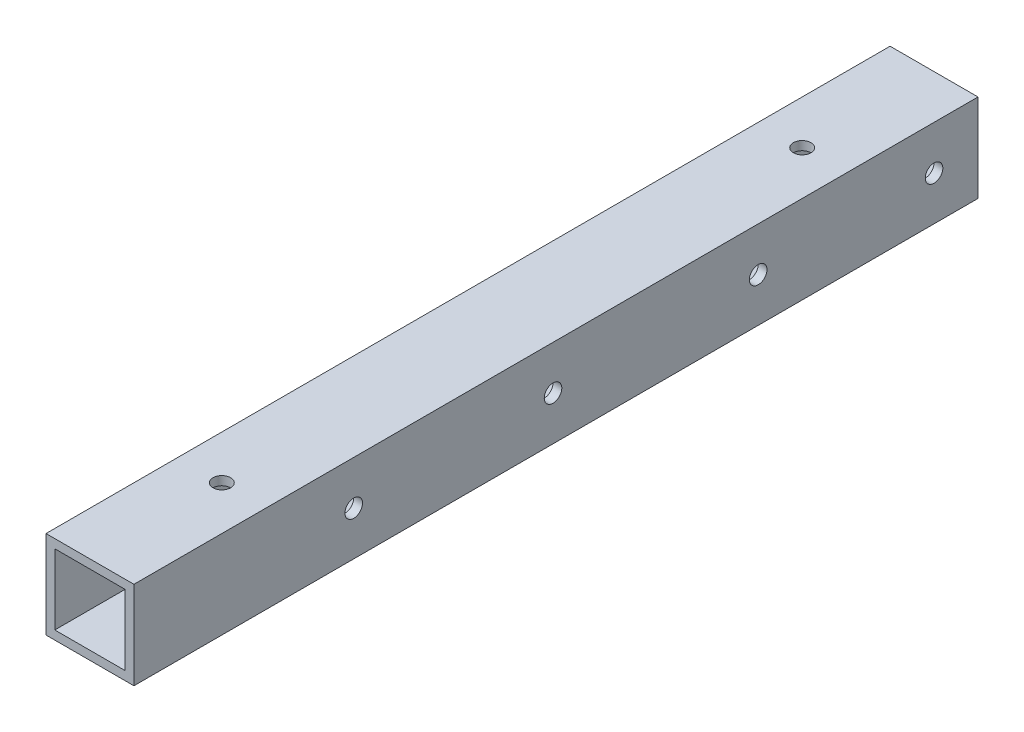
SolidWorks part; units mm, degrees
material "1060 合金"
ref_plane "正面" through (0, 0, 0) normal (0, 0, 1) x (1, 0, 0)
ref_plane "平面" through (0, 0, 0) normal (0, 1, 0) x (1, 0, 0)
ref_plane "右側面" through (0, 0, 0) normal (1, 0, 0) x (0, 0, -1)
sketch "ｽｹｯﾁ1" plane through (0, 0, 0) normal (0, 0, 1) x (1, 0, 0)
  line L1 (-7.0101, 7.7326) -> (7.9899, 7.7326)
  line L2 (-7.0101, 7.7326) -> (-7.0101, -7.2674)
  line L3 (-7.0101, -7.2674) -> (7.9899, -7.2674)
  line L4 (7.9899, 7.7326) -> (7.9899, -7.2674)
  line L9 (-5.5101, 6.2326) -> (6.4899, 6.2326)
  line L10 (-5.5101, 6.2326) -> (-5.5101, -5.7674)
  line L11 (-5.5101, -5.7674) -> (6.4899, -5.7674)
  line L12 (6.4899, 6.2326) -> (6.4899, -5.7674)
  dimension "D1" = 15
  dimension "D2" = 15
  dimension "D3" = 1.5
  dimension "D4" = 1.5
  dimension "D5" = 12
  dimension "D6" = 12
extrude "ﾎﾞｽ - 押し出し2" add sketch "ｽｹｯﾁ1" along normal blind 144
sketch "ｽｹｯﾁ3" plane through (0, 7.7326, 0) normal (0, 1, 0) x (1, 0, 0)
  line L0 (0.4899, 0) -> (0.4899, -22.5)
  line L1 (-7.0101, -144) -> (-7.0101, 0) construction
  circle A0 centre (0.4899, -22.5) radius 1.5
  dimension "D2" = 7.5
  dimension "D1" = 22.5
extrude "ｶｯﾄ - 押し出し2" cut sketch "ｽｹｯﾁ3" against normal blind 10
sketch "ｽｹｯﾁ4" plane through (0, 7.7326, 0) normal (0, 1, 0) x (1, 0, 0)
  line L0 (0.4899, -144) -> (0.4899, -121.5)
  line L2 (-7.0101, -144) -> (-7.0101, 0) construction
  circle A0 centre (0.4899, -121.5) radius 1.5
  dimension "D2" = 7.5
  dimension "D1" = 22.5
extrude "ｶｯﾄ - 押し出し4" cut sketch "ｽｹｯﾁ4" against normal blind 10
sketch "ｽｹｯﾁ7" plane through (0, -7.2674, 0) normal (0, -1, 0) x (1, 0, 0)
  line L0 (0.4899, 0) -> (0.4899, 22.5)
  line L1 (-7.0101, 0) -> (7.9899, 0) construction
  circle A0 centre (0.4899, 22.5) radius 4
  dimension "D1" = 22.5
extrude "ｶｯﾄ - 押し出し6" cut sketch "ｽｹｯﾁ7" against normal blind 10
sketch "ｽｹｯﾁ8" plane through (0, -7.2674, 0) normal (0, -1, 0) x (1, 0, 0)
  line L0 (0.4899, 144) -> (0.4899, 121.5)
  line L1 (-7.0101, 144) -> (7.9899, 144) construction
  circle A0 centre (0.4899, 121.5) radius 4
  dimension "D1" = 22.5
extrude "ｶｯﾄ - 押し出し7" cut sketch "ｽｹｯﾁ8" against normal blind 10
sketch "ｽｹｯﾁ9" plane through (-7.0101, 0, 0) normal (-1, 0, 0) x (0, 0, 1)
  line L0 (0, 0.2326) -> (37.5, 0.2326)
  line L1 (0, 7.7326) -> (0, -7.2674) construction
  circle A0 centre (37.5, 0.2326) radius 6
  dimension "D1" = 37.5
extrude "ｶｯﾄ - 押し出し8" cut sketch "ｽｹｯﾁ9" against normal blind 10
sketch "ｽｹｯﾁ10" plane through (7.9899, 0, 0) normal (1, 0, 0) x (0, 0, -1)
  line L0 (0, -7.2674) -> (0, 7.7326) construction
  line L1 (-144, 7.7326) -> (0, 7.7326) construction
  circle A0 centre (-37.5, 0.2326) radius 1.5
  dimension "D1" = 37.5
  dimension "D2" = 7.5
extrude "ｶｯﾄ - 押し出し9" cut sketch "ｽｹｯﾁ10" against normal blind 10
sketch "ｽｹｯﾁ11" plane through (0, -7.2674, 0) normal (0, -1, 0) x (1, 0, 0)
  line L0 (-7.0101, 144) -> (-7.0101, 0) construction
  line L1 (-7.0101, 0) -> (7.9899, 0) construction
  circle A0 centre (0.4899, 72.5) radius 4
  dimension "D1" = 7.5
  dimension "D2" = 72.5
extrude "ｶｯﾄ - 押し出し10" cut sketch "ｽｹｯﾁ11" against normal blind 10
sketch "ｽｹｯﾁ12" plane through (-7.0101, 0, 0) normal (-1, 0, 0) x (0, 0, 1)
  line L0 (144, 7.7326) -> (0, 7.7326) construction
  line L1 (144, 7.7326) -> (144, -7.2674) construction
  circle A0 centre (106.5, 0.2326) radius 6
  dimension "D1" = 7.5
  dimension "D2" = 37.5
extrude "ｶｯﾄ - 押し出し11" cut sketch "ｽｹｯﾁ12" against normal blind 10
sketch "ｽｹｯﾁ13" plane through (7.9899, 0, 0) normal (1, 0, 0) x (0, 0, -1)
  line L0 (-144, -7.2674) -> (-144, 7.7326) construction
  line L1 (-144, 7.7326) -> (0, 7.7326) construction
  circle A0 centre (-106.5, 0.2326) radius 1.5
  dimension "D1" = 37.5
  dimension "D2" = 7.5
extrude "ｶｯﾄ - 押し出し12" cut sketch "ｽｹｯﾁ13" against normal blind 10
sketch "ｽｹｯﾁ14" plane through (7.9899, 0, 0) normal (1, 0, 0) x (0, 0, -1)
  line L0 (-144, 7.7326) -> (0, 7.7326) construction
  line L1 (0, -7.2674) -> (0, 7.7326) construction
  circle A0 centre (-7.5, 0.2326) radius 1.5
  dimension "D1" = 7.5
  dimension "D2" = 7.5
extrude "ｶｯﾄ - 押し出し13" cut sketch "ｽｹｯﾁ14" against normal blind 10
sketch "ｽｹｯﾁ15" plane through (7.9899, 0, 0) normal (1, 0, 0) x (0, 0, -1)
  line L0 (-144, -7.2674) -> (-144, 7.7326) construction
  line L1 (-144, -7.2674) -> (0, -7.2674) construction
  circle A0 centre (-72.5, 0.2326) radius 1.5
  dimension "D1" = 71.5
  dimension "D2" = 7.5
extrude "ｶｯﾄ - 押し出し14" cut sketch "ｽｹｯﾁ15" against normal blind 10
